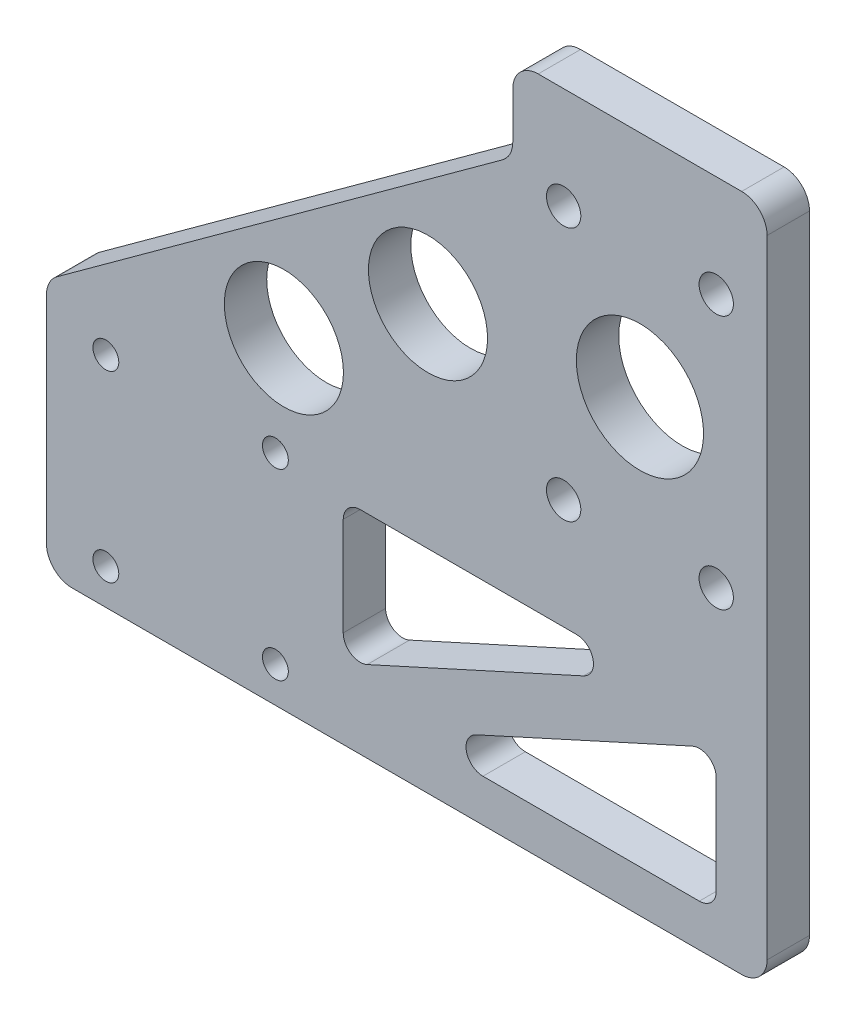
SolidWorks part; units mm, degrees
material "Thornel Mat VMA"
ref_plane "前视基准面" through (0, 0, 0) normal (0, 0, 1) x (1, 0, 0)
ref_plane "上视基准面" through (0, 0, 0) normal (0, 1, 0) x (1, 0, 0)
ref_plane "右视基准面" through (0, 0, 0) normal (1, 0, 0) x (0, 0, -1)
other "Configuration Table"
sketch "草图1" plane through (0, 0, 0) normal (0, 0, 1) x (1, 0, 0)
  line L0 (0, 0) -> (-55, 0)
  line L1 (-55, 0) -> (-55, -30)
  line L2 (-55, -30) -> (30, -30)
  line L3 (30, -30) -> (30, 50)
  line L4 (30, 50) -> (0, 50)
  line L5 (0, 50) -> (0, 0)
  dimension "D1" = 30
  dimension "D2" = 30
  dimension "D3" = 50
  dimension "D4" = 55
extrude "凸台-拉伸1" add sketch "草图1" along normal blind 5
sketch "草图2" plane through (0, 0, 5) normal (0, 0, 1) x (1, 0, 0)
  line L0 (0, 40) -> (-45, 0)
  line L1 (0, 50) -> (0, 0) construction
  line L2 (0, 0) -> (-55, 0) construction
  line L3 (0, 40) -> (0, 0)
  line L4 (0, 0) -> (-45, 0)
  dimension "D1" = 10
  dimension "D2" = 10
extrude "凸台-拉伸2" add sketch "草图2" against normal up to surface (5 mm away) up to face at (-8.3333, 6.6667, 0)
sketch "草图4" plane through (0, 0, 5) normal (0, 0, 1) x (1, 0, 0)
  line L0 (0, 33.3102) -> (0, 0)
  line L1 (0, 0) -> (-37.474, 0)
  line L2 (-37.474, 0) -> (0, 33.3102)
  line L3 (0, 40) -> (-45, 0) construction
  dimension "D1" = 5
extrude "切除-拉伸1" cut sketch "草图4" against normal up to surface (5 mm away) up to face at (-13.5714, 11.4286, 0)
sketch "草图5" plane through (0, 0, 0) normal (0, 0, -1) x (-1, 0, 0)
  circle A0 centre (48, -4.2) radius 1.525
  circle A1 centre (48, -25.8) radius 1.525
  circle A2 centre (28, -4.2) radius 1.525
  circle A3 centre (28, -25.8) radius 1.525
  circle A4 centre (48, -25.8) radius 1.525 construction
  circle A5 centre (48, -4.2) radius 1.525 construction
  circle A6 centre (28, -25.8) radius 1.525 construction
  circle A7 centre (28, -4.2) radius 1.525 construction
  dimension "D1" = 3.05
extrude "切除-拉伸2" cut sketch "草图5" against normal up to surface (35 mm away)
sketch "草图6" plane through (0, 0, 0) normal (0, 0, -1) x (-1, 0, 0)
  line L0 (-30, 50) -> (0, 50) construction
  line L1 (37.474, 0) -> (0, 0) construction
  line L2 (-15, 38) -> (-15, 8) construction
  line L3 (-24, 8) -> (-6, 8) construction
  line L4 (-24, 8) -> (-24, 38) construction
  line L5 (-24, 38) -> (-6, 38) construction
  line L6 (-6, 8) -> (-6, 38) construction
  line L7 (-24, 8) -> (-6, 38) construction
  line L8 (-24, 38) -> (-6, 8) construction
  circle A0 centre (-15, 8) radius 2.025 construction
  circle A1 centre (-15, 38) radius 2.025 construction
  circle A2 centre (-6, 38) radius 2.025
  circle A3 centre (-24, 38) radius 2.025
  circle A4 centre (-24, 8) radius 2.025
  circle A5 centre (-6, 8) radius 2.025
  point P6 (-15, 50)
  point P9 (-15, 23)
  dimension "D1" = 4.05
  dimension "D2" = 30
  dimension "D3" = 8
  dimension "D6" = 4.05
  dimension "D4" = 30
  dimension "D5" = 18
extrude "切除-拉伸3" cut sketch "草图6" against normal through all both and the other way through all
sketch "草图7" plane through (0, 0, 0) normal (0, 0, -1) x (-1, 0, 0)
  line L0 (37.474, 0) -> (0, 0) construction
  line L1 (-24, -5) -> (20, -5)
  line L2 (-24, -5) -> (-24, -25)
  line L3 (-24, -25) -> (20, -25)
  line L4 (20, -5) -> (20, -25)
  line L5 (55, -30) -> (-30, -30) construction
  line L6 (-30, -30) -> (-30, 50) construction
  line L7 (-24, -5) -> (20, -25)
  line L8 (-25.2414, -7.7311) -> (18.7586, -27.7311)
  line L9 (-22.7586, -2.2689) -> (21.2414, -22.2689)
  circle A0 centre (28, -4.2) radius 1.525 construction
  dimension "D1" = 5
  dimension "D2" = 5
  dimension "D3" = 6
  dimension "D4" = 8
  dimension "D5" = 3
  dimension "D6" = 3
extrude "切除-拉伸4" cut sketch "草图7" against normal through all contours L8 L2 L3 | L1 L9 L4
fillet "圆角4" radius 2 6 edges at (-20, -5, 2.5) (-20, -21.7046, 2.5) (16.7502, -5, 2.5) (-12.7502, -25, 2.5) (24, -25, 2.5) (24, -8.2954, 2.5)
sketch "草图8" plane through (0, 0, 0) normal (0, 0, -1) x (-1, 0, 0)
  line L1 (-24, 38) -> (-6, 38) construction
  line L2 (-24, 38) -> (-24, 8) construction
  line L3 (-24, 8) -> (-6, 8) construction
  line L4 (-6, 38) -> (-6, 8) construction
  circle A0 centre (-15, 23) radius 7.5
  point P9 (-15, 8)
  point P10 (-6, 23)
  dimension "D1" = 15
extrude "切除-拉伸5" cut sketch "草图8" against normal up to surface (5 mm away) up to face at (13.7801, -19.1897, 5)
sketch "草图9" plane through (0, 0, 5) normal (0, 0, 1) x (1, 0, 0)
  line L0 (-55, 0) -> (0, 40)
  line L1 (-55, 0) -> (0, 0)
  line L2 (0, 0) -> (0, 40)
extrude "凸台-拉伸3" add sketch "草图9" against normal up to surface (5 mm away) up to face at (7.5, 23, 0)
sketch "草图10" plane through (0, 0, 5) normal (0, 0, 1) x (1, 0, 0)
  line L0 (-55, 0) -> (-55, -30) construction
  line L1 (-55, -30) -> (30, -30) construction
  circle A0 centre (-27, 8) radius 7.025
  circle A1 centre (-10, 20) radius 7.025
  point P4 (-26.2609, 7.9298)
  point P5 (-6.7764, 19.3769)
  point P6 (-23.119, 12.2497)
  point P7 (-26.6956, 8.2836)
  dimension "D1" = 14.05
  dimension "D2" = 28
  dimension "D3" = 38
  dimension "D4" = 50
  dimension "D5" = 45
extrude "切除-拉伸6" cut sketch "草图10" against normal up to surface (5 mm away) up to face at (-8.3333, 13.3333, 0)
fillet "圆角5" radius 3 6 edges at (-55, -30, 2.5) (30, -30, 2.5) (30, 50, 2.5) (0, 50, 2.5) (-55, 0, 2.5) (0, 40, 2.5)
